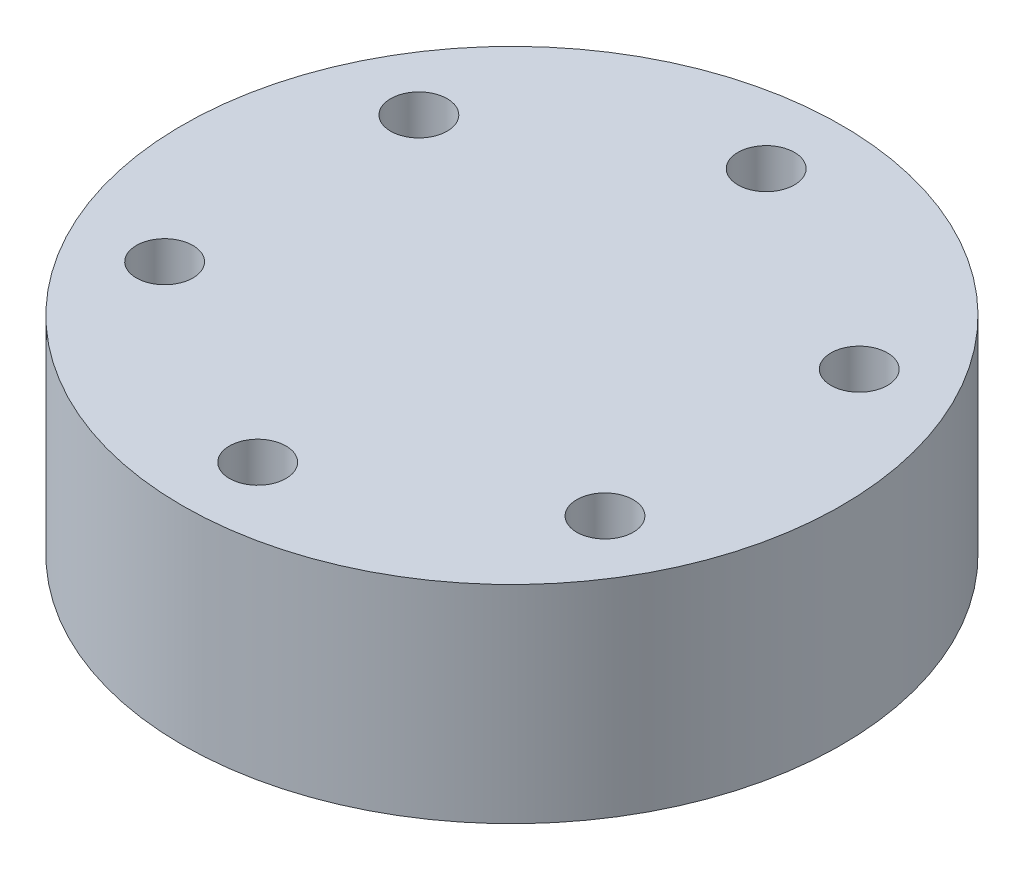
SolidWorks part; units mm, degrees
ref_plane "前视基准面" through (0, 0, 0) normal (0, 0, 1) x (1, 0, 0)
ref_plane "上视基准面" through (0, 0, 0) normal (0, 1, 0) x (1, 0, 0)
ref_plane "右视基准面" through (0, 0, 0) normal (1, 0, 0) x (0, 0, -1)
sketch "草图1" plane through (0, 0, 0) normal (0, 1, 0) x (1, 0, 0)
  circle A0 centre (0, 0) radius 17.5
  dimension "D1" = 35
extrude "凸台-拉伸1" add sketch "草图1" along normal blind 11
sketch "草图2" plane through (0, 11, 0) normal (0, 1, 0) x (1, 0, 0)
  circle A0 centre (0, 0) radius 13.5 construction
  circle A1 centre (0, 13.5) radius 1.5
  circle A2 centre (11.6913, 6.75) radius 1.5
  circle A3 centre (11.6913, -6.75) radius 1.5
  circle A4 centre (0, -13.5) radius 1.5
  circle A5 centre (-11.6913, -6.75) radius 1.5
  circle A6 centre (-11.6913, 6.75) radius 1.5
  point P18 (0, 0)
  dimension "D1" = 27
  dimension "D2" = 3
  dimension "D3" = 6
extrude "切除-拉伸1" cut sketch "草图2" against normal blind 11
